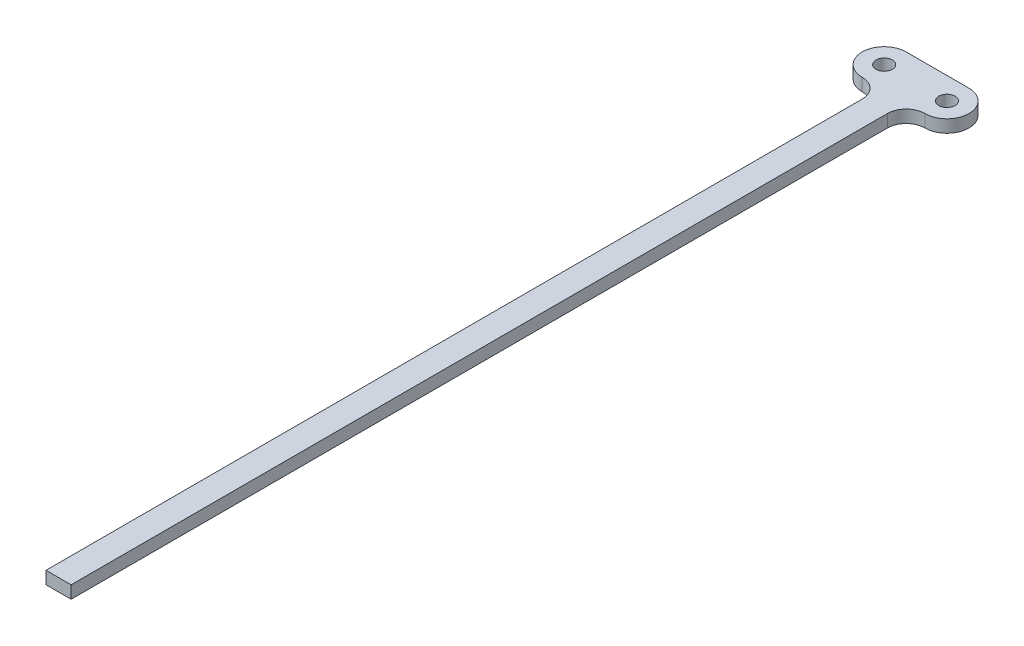
SolidWorks part; units mm, degrees
ref_plane "Front Plane" through (0, 0, 0) normal (0, 0, 1) x (1, 0, 0)
ref_plane "Top Plane" through (0, 0, 0) normal (0, 1, 0) x (1, 0, 0)
ref_plane "Right Plane" through (0, 0, 0) normal (1, 0, 0) x (0, 0, -1)
sketch "Sketch1" plane through (0, 0, 0) normal (0, 1, 0) x (1, 0, 0)
  line L0 (0, 0) -> (5.08, 0)
  line L1 (5.08, 0) -> (5.08, 165.1)
  line L2 (0, 0) -> (0, 165.1)
  line L3 (-3.81, 177.8) -> (8.89, 177.8)
  line L6 (2.54, 177.8) -> (2.54, 0) construction
  arc A2 (0, 165.1) -> (-3.81, 168.91) centre (-3.81, 165.1) ccw
  arc A3 (5.08, 165.1) -> (8.89, 168.91) centre (8.89, 165.1) cw
  arc A4 (-3.81, 168.91) -> (-3.81, 177.8) centre (-3.81, 173.355) cw
  arc A5 (8.89, 168.91) -> (8.89, 177.8) centre (8.89, 173.355) ccw
  circle A6 centre (-3.81, 173.355) radius 1.651
  circle A7 centre (8.89, 173.355) radius 1.651
  dimension "D1" = 3.302
  dimension "D2" = 3.302
  dimension "D3" = 5.08
  dimension "D4" = 12.7
  dimension "D5" = 177.8
  dimension "D6" = 165.1
extrude "Boss-Extrude1" add sketch "Sketch1" along normal blind 2.54
